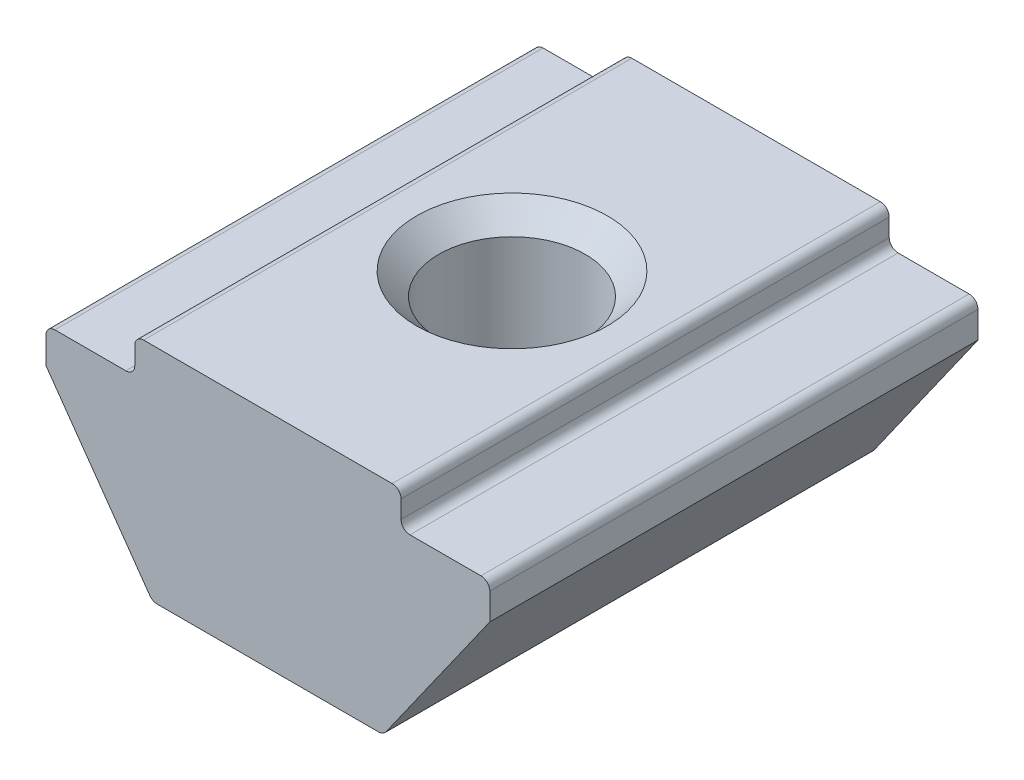
SolidWorks part; units mm, degrees
ref_plane "Спереди" through (0, 0, 0) normal (0, 0, 1) x (1, 0, 0)
ref_plane "Сверху" through (0, 0, 0) normal (0, 1, 0) x (1, 0, 0)
ref_plane "Справа" through (0, 0, 0) normal (1, 0, 0) x (0, 0, -1)
sketch "Эскиз1" plane through (0, 0, 0) normal (0, 0, 1) x (1, 0, 0)
  line L0 (3, 0) -> (-3, 0)
  line L1 (-3, 0) -> (-3, -0.8)
  line L2 (-3, -0.8) -> (-5, -0.8)
  line L3 (-5, -0.8) -> (-5, -1.6)
  line L4 (-5, -1.6) -> (-2.6, -5)
  line L5 (-2.6, -5) -> (2.6, -5)
  line L6 (0, -5) -> (0, 0) construction
  line L7 (5, -1.6) -> (2.6, -5)
  line L8 (5, -0.8) -> (5, -1.6)
  line L9 (3, -0.8) -> (5, -0.8)
  line L10 (3, 0) -> (3, -0.8)
  point P3 (-3, -0.4)
  point P9 (0, 0)
  dimension "D1" = 6
  dimension "D2" = 10
  dimension "D3" = 5.2
  dimension "D4" = 5
  dimension "D5" = 4.2
extrude "Бобышка-Вытянуть1" add sketch "Эскиз1" along normal mid plane 11
hole_wizard "Отверстие обработанное метчиком M41" positions "Эскиз2" profile "Эскиз4" tap size "M4" standard "ISO" end condition through all
sketch "Эскиз2" plane through (0, 0, 0) normal (0, 1, 0) x (1, 0, 0)
  point P0 (0, 0)
sketch "Эскиз4" plane through (0, 0, 0) normal (1, 0, 0) x (0, 0, 1)
  line L0 (0, 0) -> (0, 5)
  line L1 (0, 5) -> (2.15, 5)
  line L2 (1.65, 4.5) -> (1.65, 0.5)
  line L3 (1.65, 0.5) -> (2.15, 0)
  line L5 (2.15, 0) -> (0, 0)
  line L6 (-1.65, 0.5) -> (-2.15, 0) construction
  line L7 (2.15, 5) -> (1.65, 4.5)
  line L8 (-2.15, 5) -> (-1.65, 4.5) construction
  line L11 (0, -6.35) -> (0, 107.95) construction
  dimension "Диаметр проходного сверла" = 3.3
  dimension "Глубина проходного сверла" = 5
  dimension "Диаметр передней зенковки" = 4.3
  dimension "Угол передней зенковки" = 90
  dimension "Диаметр задней зенковки" = 4.3
  dimension "Угол задней зенковки" = 90
cosmetic thread "Отверстие резьбы1" parameters "D2"=4
fillet "Скругление1" radius 0.2 8 edges at (2.6, -5, 0) (-2.6, -5, 0) (5, -0.8, 0) (3, -0.8, 0) (3, 0, 0) (-3, 0, 0) (-5, -0.8, 0) (-3, -0.8, 0)
